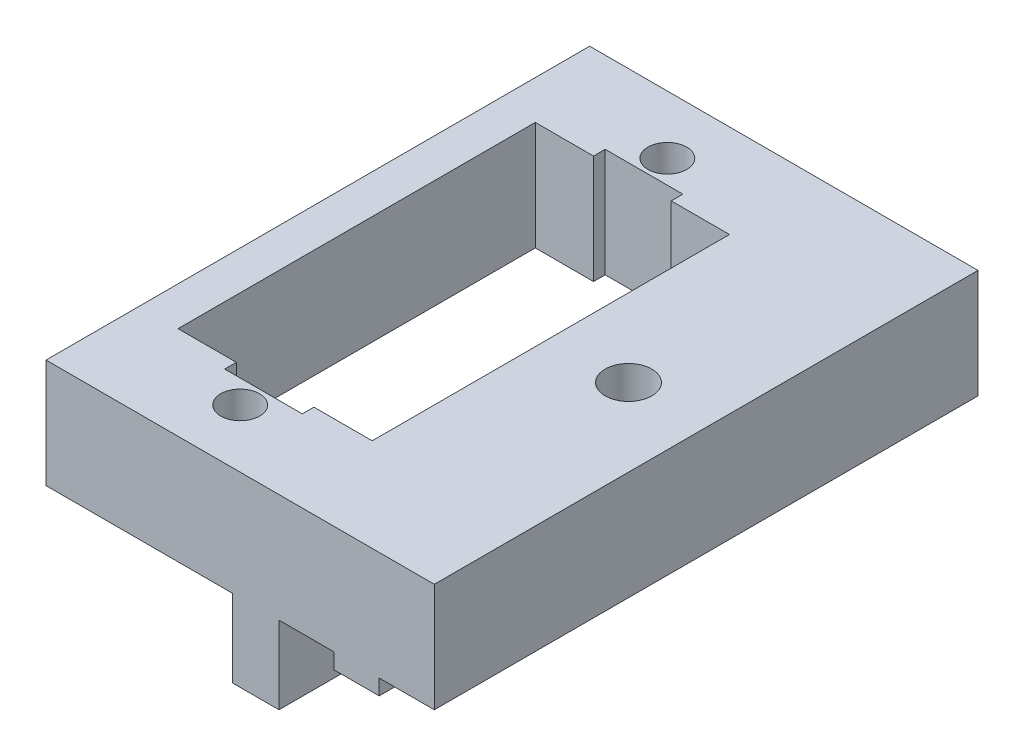
SolidWorks part; units mm, degrees
ref_plane "Front Plane" through (0, 0, 0) normal (0, 0, 1) x (1, 0, 0)
ref_plane "Top Plane" through (0, 0, 0) normal (0, 1, 0) x (1, 0, 0)
ref_plane "Right Plane" through (0, 0, 0) normal (1, 0, 0) x (0, 0, -1)
sketch "Sketch1" plane through (0, 0, 0) normal (0, 0, 1) x (1, 0, 0)
  line L0 (10, 0) -> (10, 7)
  line L1 (10, 7) -> (-15, 7)
  line L2 (-15, 7) -> (-15, 0)
  line L3 (-15, 0) -> (-3, 0)
  line L4 (3.55, 0) -> (3.55, -1)
  line L5 (3.55, -1) -> (6.45, -1)
  line L6 (6.45, -1) -> (6.45, 0)
  line L7 (6.45, 0) -> (10, 0)
  line L8 (-3, 0) -> (-3, -5)
  line L9 (-3, -5) -> (0, -5)
  line L10 (0, -5) -> (0, 0)
  line L11 (0, 0) -> (3.55, 0)
  dimension "D1" = 10
  dimension "D2" = 1
  dimension "D3" = 7
  dimension "D4" = 2.9
  dimension "D5" = 3.55
  dimension "D6" = 15
  dimension "D7" = 3
  dimension "D8" = 5
extrude "Main" add sketch "Sketch1" along normal mid plane 35
sketch "Sketch2" plane through (0, 7, 0) normal (0, 1, 0) x (1, 0, 0)
  line L0 (10, -17.5) -> (10, 17.5) construction
  line L1 (-6.25, -13.75) -> (-6.25, 13.75) construction
  circle A0 centre (5, 0) radius 1.5
  circle A1 centre (-6.25, 13.75) radius 1.25
  circle A2 centre (-6.25, -13.75) radius 1.25
  point P9 (-6.25, 0)
  dimension "D1" = 3
  dimension "D3" = 2.5
  dimension "D2" = 5
  dimension "D4" = 6.25
  dimension "D5" = 27.5
extrude "FixingHole" cut sketch "Sketch2" against normal through all
sketch "Sketch3" plane through (0, 7, 0) normal (0, 1, 0) x (1, 0, 0)
  line L1 (-12.5, 11.5) -> (0, 11.5)
  line L2 (-12.5, 11.5) -> (-12.5, -11.5)
  line L3 (-12.5, -11.5) -> (0, -11.5)
  line L4 (0, 11.5) -> (0, -11.5)
  point P6 (0, 0)
  dimension "D1" = 23
  dimension "D2" = 12.5
extrude "ServoSquareHole" cut sketch "Sketch3" against normal through all
sketch "Sketch4" plane through (0, 7, 0) normal (0, 1, 0) x (1, 0, 0)
  line L0 (0, 11.5) -> (-12.5, 11.5) construction
  line L1 (-3.75, -12.25) -> (-8.75, -12.25)
  line L2 (-3.75, -12.25) -> (-3.75, 12.25)
  line L3 (-3.75, 12.25) -> (-8.75, 12.25)
  line L4 (-8.75, -12.25) -> (-8.75, 12.25)
  line L5 (-12.5, -11.5) -> (0, -11.5) construction
  point P8 (-6.25, -11.5)
  point P9 (-6.25, -12.25)
  point P10 (0, 0)
  dimension "D1" = 0.75
  dimension "D2" = 0.75
  dimension "D3" = 5
extrude "CableHole" cut sketch "Sketch4" against normal through all
